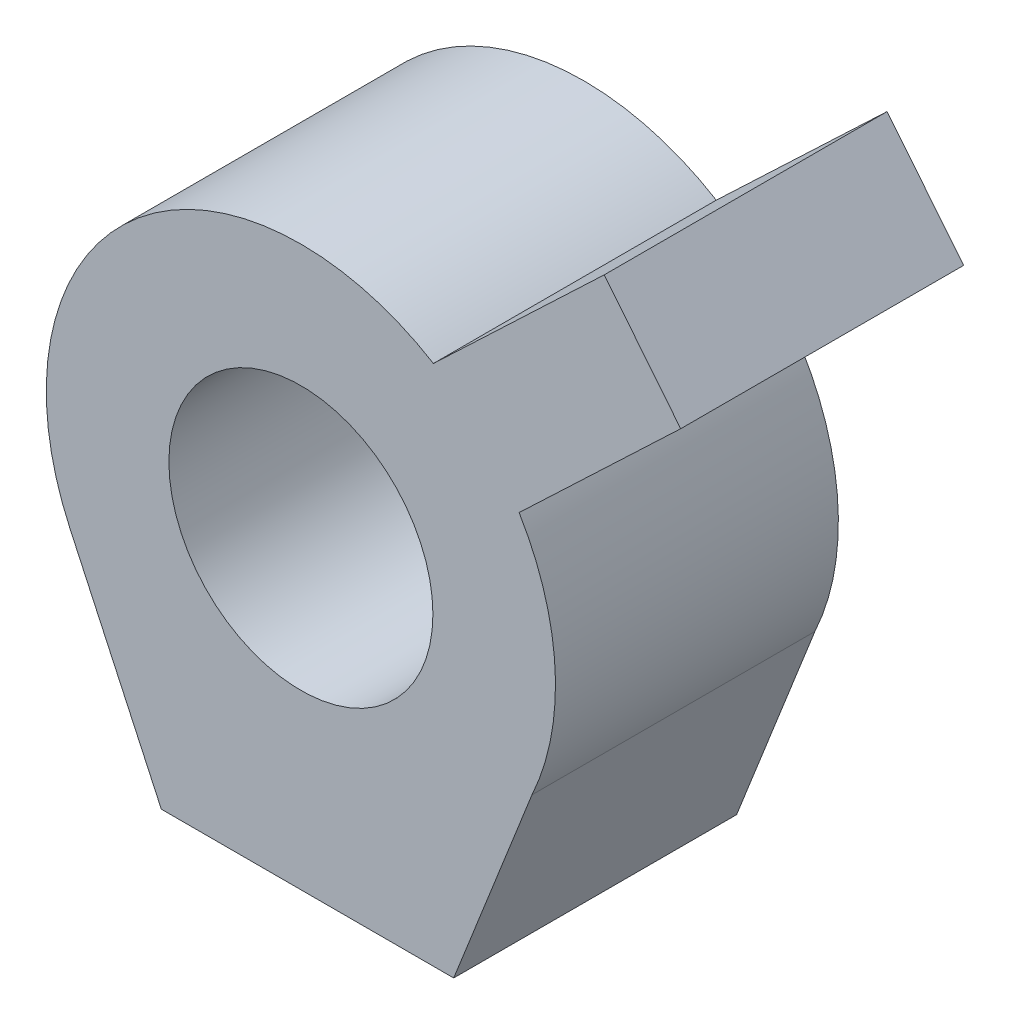
SolidWorks part; units mm, degrees
ref_plane "Front Plane" through (0, 0, 0) normal (0, 0, 1) x (1, 0, 0)
ref_plane "Top Plane" through (0, 0, 0) normal (0, 1, 0) x (1, 0, 0)
ref_plane "Right Plane" through (0, 0, 0) normal (1, 0, 0) x (0, 0, -1)
sketch "Sketch1" plane through (0, 0, 0) normal (0, 0, 1) x (1, 0, 0)
  line L0 (-19.4506, -8.9985) -> (-11.7497, -25.6443)
  line L1 (-11.7497, -25.6443) -> (12.8632, -25.6443)
  line L2 (12.8632, -25.6443) -> (19.4506, -8.9985)
  line L3 (11.1539, 18.3) -> (25.5351, 31.9517)
  line L4 (31.9705, 23.9509) -> (25.5351, 31.9517)
  line L5 (31.9705, 23.9509) -> (18.3692, 11.0395)
  circle A0 centre (0, 0) radius 11.1125
  arc A1 (19.4506, -8.9985) -> (18.3692, 11.0395) centre (0, 0) ccw
  arc A2 (11.1539, 18.3) -> (-19.4506, -8.9985) centre (0, 0) ccw
  point P10 (17.8117, 11.9181)
  point P12 (23.9637, 31.2969)
  point P13 (32.0826, 23.8328)
  point P14 (25.5351, 31.9517)
  point P15 (0, 0)
  point P16 (0, 0)
  point P17 (0, 0)
  point P18 (0, 0)
  dimension "D1" = 22.225
  dimension "D2" = 42.8625
extrude "Boss-Extrude1" add sketch "Sketch1" along normal blind 23.8125
